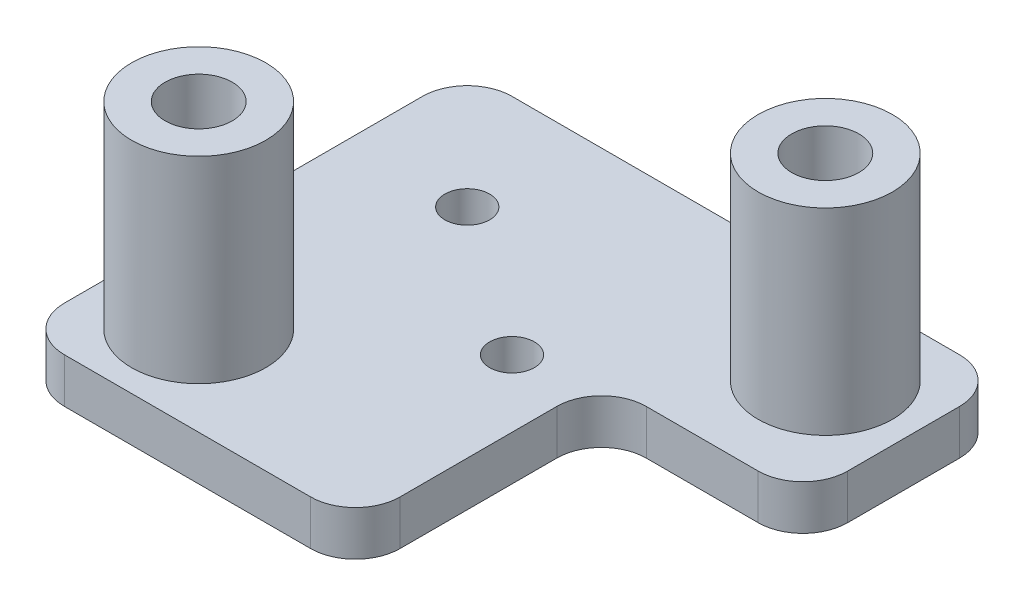
SolidWorks part; units mm, degrees
ref_plane "Alzado" through (0, 0, 0) normal (0, 0, 1) x (1, 0, 0)
ref_plane "Planta" through (0, 0, 0) normal (0, 1, 0) x (1, 0, 0)
ref_plane "Vista lateral" through (0, 0, 0) normal (1, 0, 0) x (0, 0, -1)
sketch "Croquis1" plane through (0, 0, 0) normal (0, 1, 0) x (1, 0, 0)
  line L0 (0, 0) -> (0, 6.7969) construction
  line L1 (-6, 5) -> (6, 5)
  line L2 (-6, 5) -> (-6, -5)
  line L4 (6, 5) -> (6, 0.5)
  line L5 (1.5, -5) -> (1.5, 0.5)
  line L6 (1.5, 0.5) -> (6, 0.5)
  line L7 (0, 0) -> (6.6455, 0) construction
  line L8 (-6, -5) -> (1.5, -5)
  circle A0 centre (4, 3) radius 1.5
  circle A2 centre (-4, -3) radius 1.5
  dimension "D3" = 3
  dimension "D4" = 2
  dimension "D5" = 2
  dimension "D6" = 4.5
  dimension "D7" = 7.5
extrude "Saliente-Extruir1" add sketch "Croquis1" along normal blind 1
sketch "Croquis2" plane through (0, 1, 0) normal (0, 1, 0) x (1, 0, 0)
  circle A0 centre (4, 3) radius 1.5
  circle A1 centre (-4, -3) radius 1.5
extrude "Saliente-Extruir2" add sketch "Croquis2" along normal blind 4.4 separate body
sketch "Croquis3" plane through (0, 5.4, 0) normal (0, 1, 0) x (1, 0, 0)
  circle A0 centre (4, 3) radius 0.75
  circle A1 centre (-4, -3) radius 0.75
  dimension "D1" = 1.5
  dimension "D2" = 1.5
extrude "Cortar-Extruir1" cut sketch "Croquis3" against normal blind 8
fillet "Redondeo1" radius 1 6 edges at (6, 0.5, -5) (-6, 0.5, -5) (1.5, 0.5, -0.5) (6, 0.5, -0.5) (1.5, 0.5, 5) (-6, 0.5, 5)
sketch "Croquis4" plane through (0, 1, 0) normal (0, -1, 0) x (1, 0, 0)
  circle A0 centre (4, -3) radius 1.5
  circle A1 centre (-4, 3) radius 1.5
  circle A2 centre (-4, 3) radius 0.75
  circle A3 centre (4, -3) radius 0.75
  dimension "D1" = 1.5
  dimension "D2" = 1.5
extrude "Saliente-Extruir3" add sketch "Croquis4" along normal blind 1
sketch "Croquis5" plane through (0, 1, 0) normal (0, 1, 0) x (1, 0, 0)
  line L0 (5, 5) -> (-5, 5) construction
  line L1 (-6, 4) -> (-6, -4) construction
  circle A0 centre (-3.36, 2.36) radius 0.5
  circle A1 centre (0, 0) radius 0.5
  dimension "D1" = 1
  dimension "D4" = 1
  dimension "D2" = 2.64
  dimension "D3" = 2.64
extrude "Cortar-Extruir2" cut sketch "Croquis5" against normal blind 1
